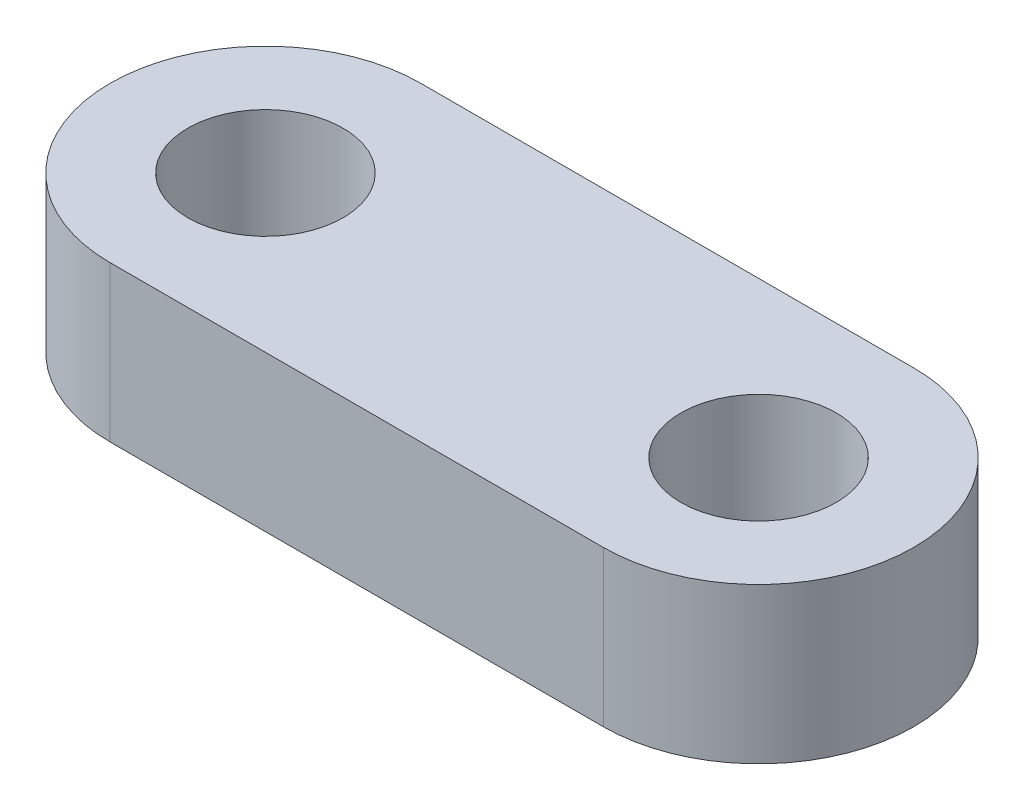
SolidWorks part; units mm, degrees
ref_plane "Front Plane" through (0, 0, 0) normal (0, 0, 1) x (1, 0, 0)
ref_plane "Top Plane" through (0, 0, 0) normal (0, 1, 0) x (1, 0, 0)
ref_plane "Right Plane" through (0, 0, 0) normal (1, 0, 0) x (0, 0, -1)
sketch "Sketch1" plane through (0, 0, 0) normal (0, 1, 0) x (1, 0, 0)
  line L0 (-3.175, 0) -> (3.175, 0) construction
  line L1 (-3.175, 2) -> (3.175, 2)
  line L2 (-3.175, -2) -> (3.175, -2)
  arc A0 (-3.175, 2) -> (-3.175, -2) centre (-3.175, 0) ccw
  arc A1 (3.175, -2) -> (3.175, 2) centre (3.175, 0) ccw
  circle A2 centre (3.175, 0) radius 1
  circle A3 centre (-3.175, 0) radius 1
  point P3 (0, 0)
  dimension "D2" = 2
  dimension "D3" = 1
  dimension "D1" = 6.35
extrude "Boss-Extrude1" add sketch "Sketch1" along normal blind 2
